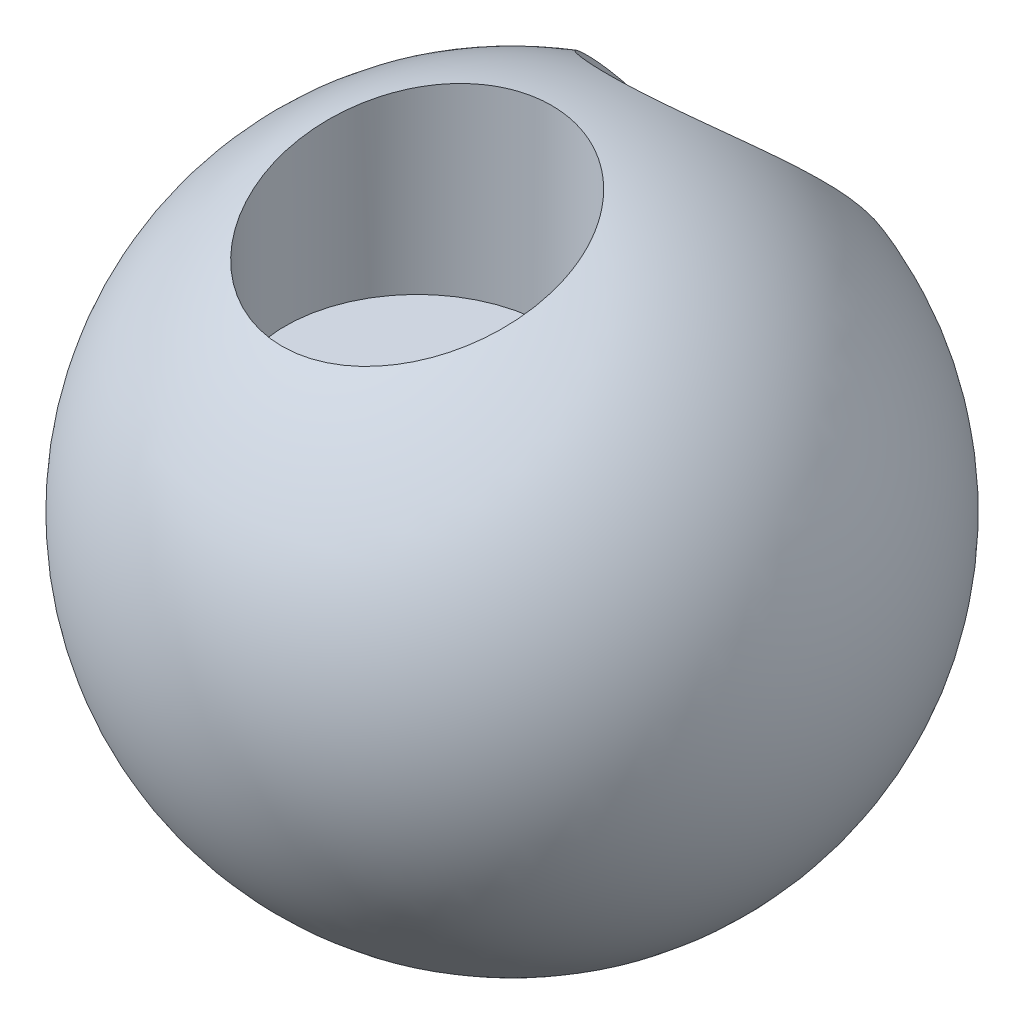
SolidWorks part; units mm, degrees
ref_plane "Front Plane" through (0, 0, 0) normal (0, 0, 1) x (1, 0, 0)
ref_plane "Top Plane" through (0, 0, 0) normal (0, 1, 0) x (1, 0, 0)
ref_plane "Right Plane" through (0, 0, 0) normal (1, 0, 0) x (0, 0, -1)
sketch "Sketch2" plane through (0, 0, 0) normal (0, 0, 1) x (1, 0, 0)
  line L0 (0, 100) -> (0, -100)
  arc A0 (0, 100) -> (0, -100) centre (0, 0) ccw
  dimension "D1" = 200
revolve "Revolve2" add sketch "Sketch2" angle 360 about L0
ref_plane "Plane2" through (0, 100, 0) normal (0, -1, 0) x (-1, 0, 0)
sketch "Sketch6" plane through (-2.538, 100, 26.2322) normal (0, -1, 0) x (-1, 0, 0)
  circle A0 centre (0, 0) radius 40
  dimension "D1" = 80
extrude "Cut-Extrude3" cut sketch "Sketch6" along normal blind 59.2948 contours A0
ref_plane "Plane4" through (0, 100, 0) normal (0, 1, 0) x (1, 0, 0)
ref_plane "Plane6" through (100, 0, 0) normal (1, 0, 0) x (0, 0, -1)
sketch "Sketch10" plane through (-2.8796, 100, -0.1784) normal (0, 1, 0) x (1, 0, 0)
  circle A0 centre (0, 71.7171) radius 35.3612
  dimension "D1" = 70.7224
extrude "Cut-Extrude6" cut sketch "Sketch10" against normal blind 199
sketch "Sketch13" plane through (0, 0, 0) normal (1, 0, 0) x (0, 0, -1)
  line L0 (0, -72.4423) -> (0, 0) construction
  line L1 (0, 0) -> (75.7393, 0) construction
  circle A0 centre (60, 0) radius 12
  dimension "D1" = 24
  dimension "D2" = 60
  dimension "D3" = 0
extrude "Cut-Extrude7" cut sketch "Sketch13" against normal mid plane 130
ref_plane "Plane8" through (0, 0, -13.7678) normal (0, 0, 1) x (1, 0, 0)
